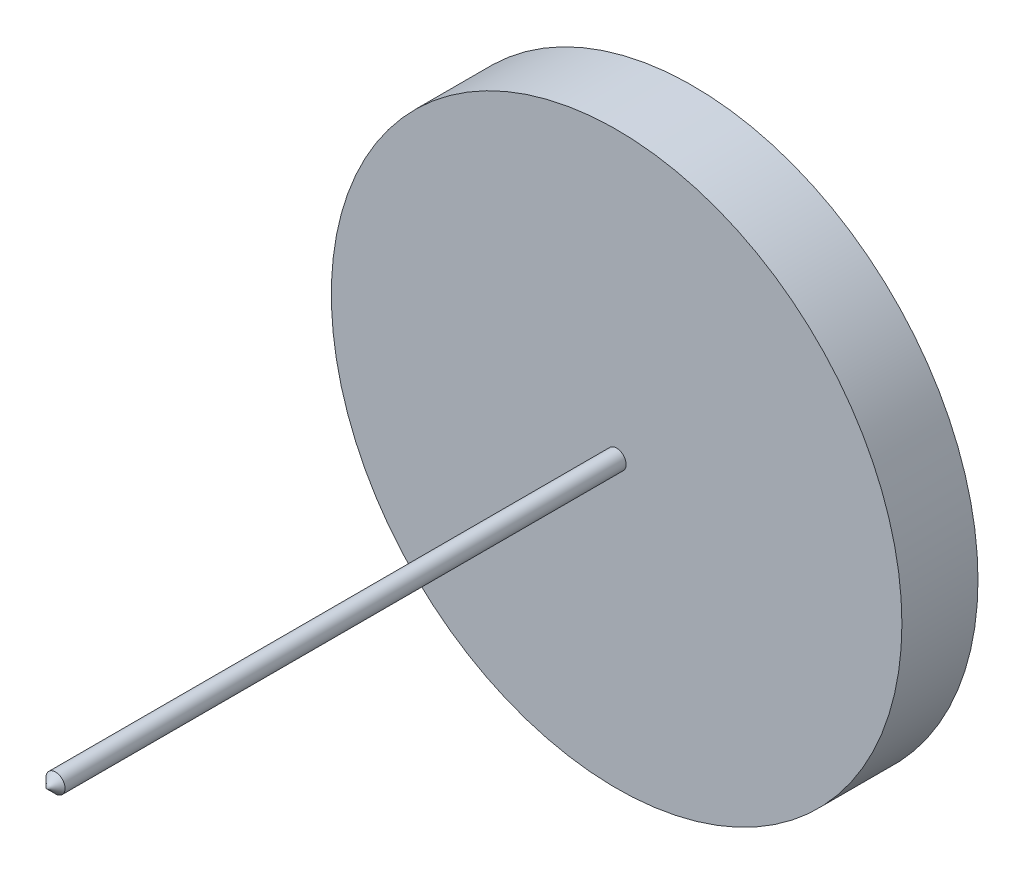
SolidWorks part; units mm, degrees
material "1023 Carbon Steel Sheet (SS)"
ref_plane "Front Plane" through (0, 0, 0) normal (0, 0, 1) x (1, 0, 0)
ref_plane "Top Plane" through (0, 0, 0) normal (0, 1, 0) x (1, 0, 0)
ref_plane "Right Plane" through (0, 0, 0) normal (1, 0, 0) x (0, 0, -1)
sketch "Sketch1" plane through (0, 0, 0) normal (0, 0, 1) x (1, 0, 0)
  circle A0 centre (0, 0) radius 7.5
  dimension "D1" = 15
extrude "Boss-Extrude1" add sketch "Sketch1" along normal blind 2
sketch "Sketch2" plane through (0, 0, 2) normal (0, 0, 1) x (1, 0, 0)
  circle A0 centre (0, 0) radius 0.25
  dimension "D1" = 0.5
extrude "Boss-Extrude2" add sketch "Sketch2" along normal blind 15
chamfer "Chamfer1" distance 0.25 angle 45 1 edges at (0.25, 0, 17)
